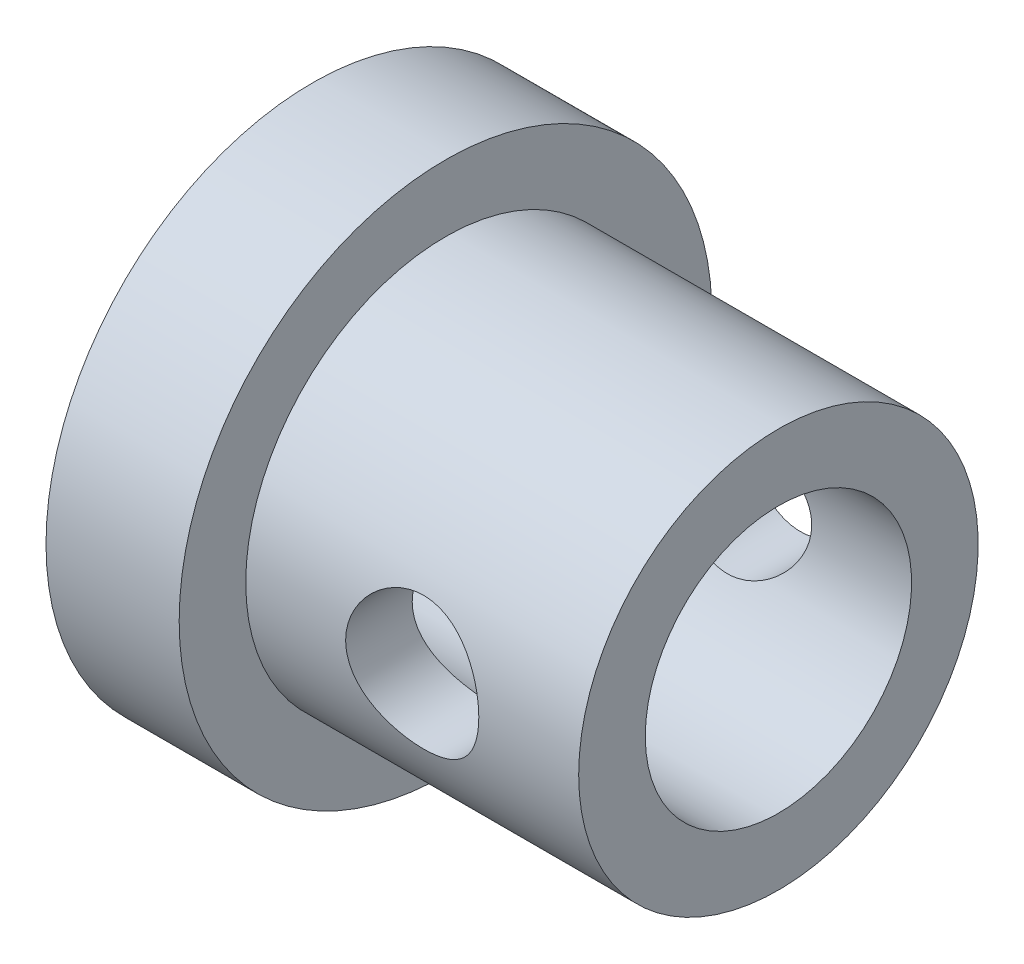
SolidWorks part; units mm, degrees
ref_plane "Front Plane" through (0, 0, 0) normal (0, 0, 1) x (1, 0, 0)
ref_plane "Top Plane" through (0, 0, 0) normal (0, 1, 0) x (1, 0, 0)
ref_plane "Right Plane" through (0, 0, 0) normal (1, 0, 0) x (0, 0, -1)
sketch "Sketch2" plane through (0, 0, 0) normal (0, 0, 1) x (1, 0, 0)
  line L0 (0, 0) -> (7, 0)
  line L1 (7, 0) -> (7, 3)
  line L2 (7, 3) -> (2, 3)
  line L3 (2, 3) -> (2, 4)
  line L4 (2, 4) -> (0, 4)
  line L5 (0, 4) -> (0, 0)
  point P3 (0, 0)
  point P8 (0, 0)
  dimension "D1" = 7
  dimension "D2" = 4
  dimension "D3" = 3
  dimension "D4" = 1
  dimension "D5" = 2
revolve "Revolve1" add sketch "Sketch2" angle 360 about L0
sketch "Sketch3" plane through (0, 0, 0) normal (-1, 0, 0) x (0, 0, 1)
  circle A0 centre (0, 0) radius 2
  dimension "D1" = 4
extrude "Cut-Extrude1" cut sketch "Sketch3" against normal through all
sketch "Sketch4" plane through (0, 0, 0) normal (0, 0, 1) x (1, 0, 0)
  line L0 (7, -3) -> (7, 3) construction
  circle A0 centre (4.5, 0) radius 1
  point P4 (0, 0)
  dimension "D1" = 2
  dimension "D2" = 2.5
extrude "Cut-Extrude2" cut sketch "Sketch4" against normal mid plane 10
